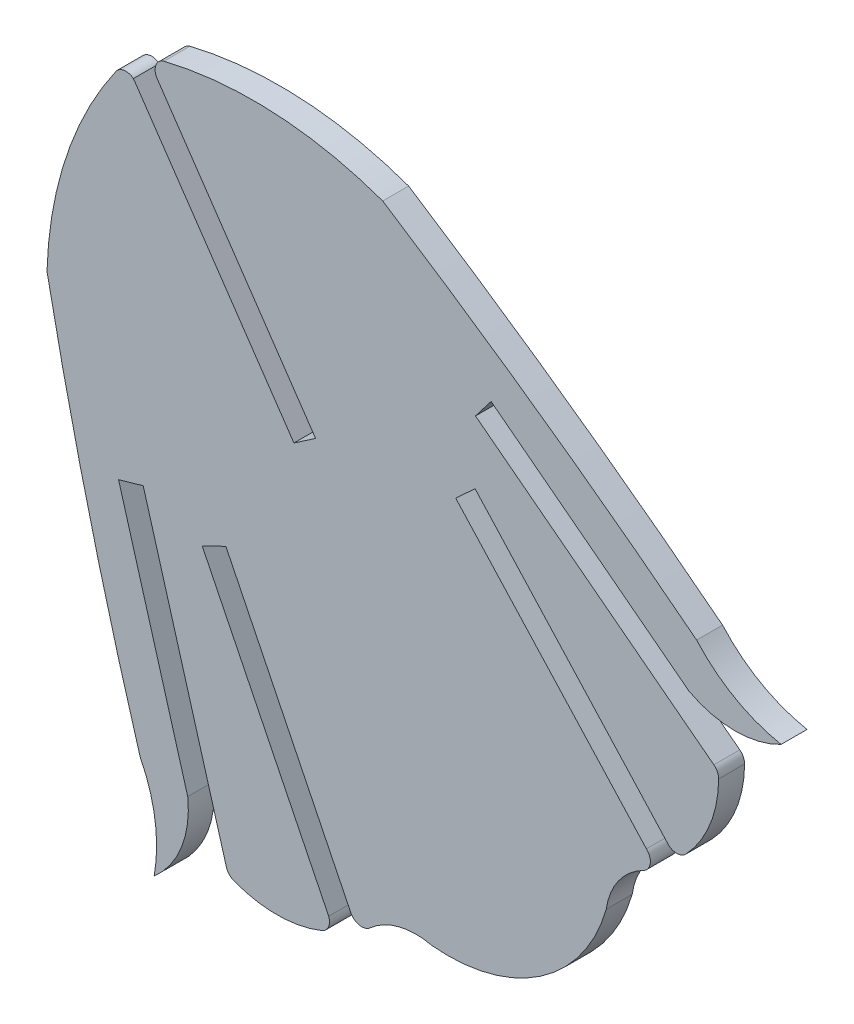
SolidWorks part; units mm, degrees
ref_plane "Front Plane" through (0, 0, 0) normal (0, 0, 1) x (1, 0, 0)
ref_plane "Top Plane" through (0, 0, 0) normal (0, 1, 0) x (1, 0, 0)
ref_plane "Right Plane" through (0, 0, 0) normal (1, 0, 0) x (0, 0, -1)
sketch "Sketch1" plane through (0, 0, 0) normal (0, 0, 1) x (1, 0, 0)
  line L0 (191.1709, 516.9947) -> (160.8156, 561.5139) construction
  line L1 (189.7773, 495.5072) -> (191.2248, 495.9246)
  line L2 (220.8167, 492.2248) -> (209.5994, 504.4838)
  line L3 (209.5994, 504.4838) -> (210.7411, 505.5285)
  line L4 (210.7411, 505.5285) -> (222.1127, 493.0784)
  line L6 (196.1192, 478.9468) -> (191.2248, 495.9246)
  line L7 (194.6964, 494.5885) -> (202.1325, 479.455)
  line L8 (196.086, 495.2697) -> (194.6964, 494.5885)
  line L9 (203.4005, 480.3496) -> (196.086, 495.2697)
  line L10 (189.7773, 495.5072) -> (193.8442, 481.4011)
  line L179 (190.6517, 516.3723) -> (200.0884, 502.5324)
  line L180 (200.0884, 502.5324) -> (201.3619, 503.401)
  line L181 (201.3619, 503.401) -> (192.0223, 517.0985)
  line L191 (224.7822, 498.4906) -> (210.7653, 509.2482)
  line L192 (210.7653, 509.2482) -> (211.6826, 510.4432)
  line L193 (211.6826, 510.4432) -> (223.3285, 501.5049)
  arc A0 (185.5688, 504.0075) -> (189.6276, 516.2321) centre (207.9187, 503.373) cw
  arc A1 (191.8696, 476.3686) -> (193.8442, 481.4011) centre (188.0666, 480.7645) ccw
  arc A2 (196.5557, 478.4718) -> (196.1192, 478.9468) centre (196.814, 479.1471) cw
  arc A3 (202.1325, 479.455) -> (201.7303, 478.522) centre (201.4589, 479.1922) cw
  arc A4 (204.5553, 480.0728) -> (203.4005, 480.3496) centre (204.0741, 480.6125) cw
  arc A5 (191.0466, 482.0259) -> (191.8696, 476.3686) centre (183.0869, 477.9795) cw
  arc A6 (185.5688, 504.0075) -> (191.0466, 482.0259) centre (413.5143, 549.138) ccw
  arc A7 (204.5553, 480.0728) -> (208.2217, 480.9952) centre (207.2707, 477.0277) cw
  arc A8 (201.7303, 478.522) -> (196.5557, 478.4718) centre (199.0792, 485.0685) cw
  arc A9 (205.3069, 517.4659) -> (223.7687, 504.3374) centre (80.0337, 321.7555) cw
  arc A10 (223.7687, 504.3374) -> (228.7345, 501.5049) centre (230.443, 510.269) ccw
  arc A11 (228.7345, 501.5049) -> (223.3285, 501.5049) centre (226.0315, 506.6507) cw
  arc A106 (208.2217, 480.9952) -> (218.4547, 487.9726) centre (209.1447, 490.634) ccw
  arc A107 (223.1282, 493.112) -> (225.065, 497.9108) centre (218.0023, 497.9712) ccw
  arc A108 (220.6526, 491.0487) -> (218.4547, 487.9726) centre (222.4954, 487.4087) ccw
  arc A589 (205.3069, 517.4659) -> (192.4444, 518.1528) centre (197.7338, 496.4286) ccw
  arc A594 (190.6517, 516.3723) -> (189.6276, 516.2321) centre (190.2082, 515.8012) ccw
  arc A595 (192.4444, 518.1528) -> (192.0223, 517.0985) centre (192.649, 517.4592) ccw
  arc A601 (220.6526, 491.0487) -> (220.8167, 492.2248) centre (220.326, 491.6938) ccw
  arc A602 (222.1127, 493.0784) -> (223.1282, 493.112) centre (222.6034, 493.6095) ccw
  arc A603 (225.065, 497.9108) -> (224.7822, 498.4906) centre (224.342, 497.917) ccw
extrude "Boss-Extrude1" add sketch "Sketch1" along normal blind 1.524
